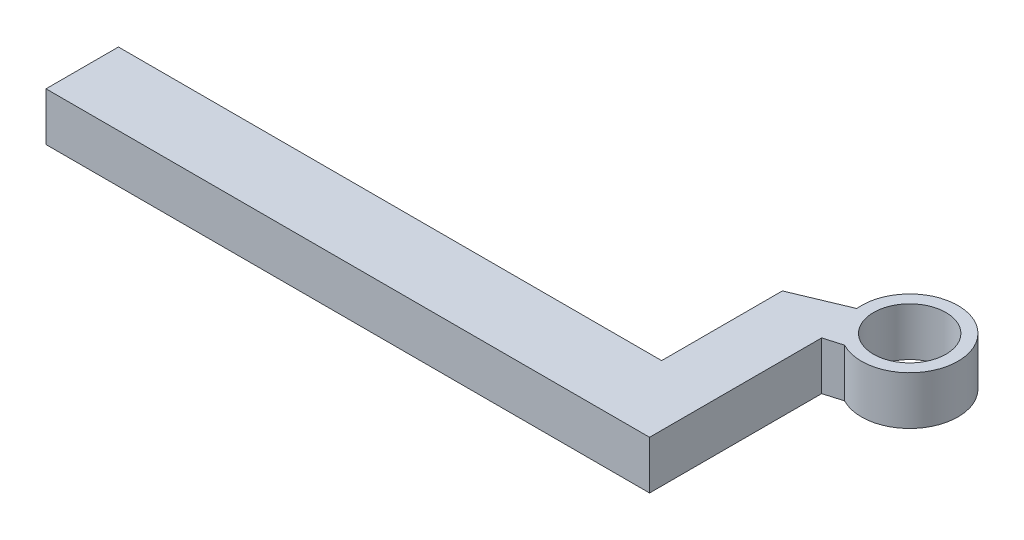
SolidWorks part; units mm, degrees
material "1060 Alloy"
ref_plane "Front Plane" through (0, 0, 0) normal (0, 0, 1) x (1, 0, 0)
ref_plane "Top Plane" through (0, 0, 0) normal (0, 1, 0) x (1, 0, 0)
ref_plane "Right Plane" through (0, 0, 0) normal (1, 0, 0) x (0, 0, -1)
sketch "Sketch2" plane through (0, 0, 0) normal (0, 1, 0) x (1, 0, 0)
  line L1 (200, 30) -> (-250, 30)
  line L2 (250, 30) -> (250, -30)
  line L3 (250, -30) -> (-250, -30)
  line L4 (-250, 30) -> (-250, -30)
  line L8 (250, 30) -> (250, 112.5737)
  line L10 (200, 30) -> (200, 130)
  arc A0 (264.6511, 116.867) -> (243.4155, 148.2002) centre (283.2045, 152.3039) ccw
  arc A1 (283.2045, 122.3039) -> (253.2045, 152.3039) centre (283.2045, 152.3039) ccw
  arc A2 (283.2045, 122.3039) -> (253.2045, 152.3039) centre (283.2045, 152.3039) cw
  spline S0 degree 2 poles (200, 130) (221.7078, 139.1001) (243.4155, 148.2002) knots 0 0 0 0.816013 0.816013 0.816013
  spline S1 degree 2 poles (250, 112.5737) (257.3255, 114.7203) (264.6511, 116.867) knots 0 0 0 0.441238 0.441238 0.441238
  point P0 (0, 0)
  dimension "D5" = 80
  dimension "D6" = 60
  dimension "D1" = 60
  dimension "D2" = 500
  dimension "D3" = 100
extrude "Boss-Extrude4" add sketch "Sketch2" along normal blind 40 contours L1 L4 L3 L2 L8 S1 A0 S0 L10
sketch "Sketch6" plane through (0, 0, 0) normal (0, -1, 0) x (1, 0, 0)
  circle A0 centre (283.2045, -152.3039) radius 30
  dimension "D1" = 60
extrude "Cut-Extrude1" cut sketch "Sketch6" against normal up to next and the other way through all contours A0
